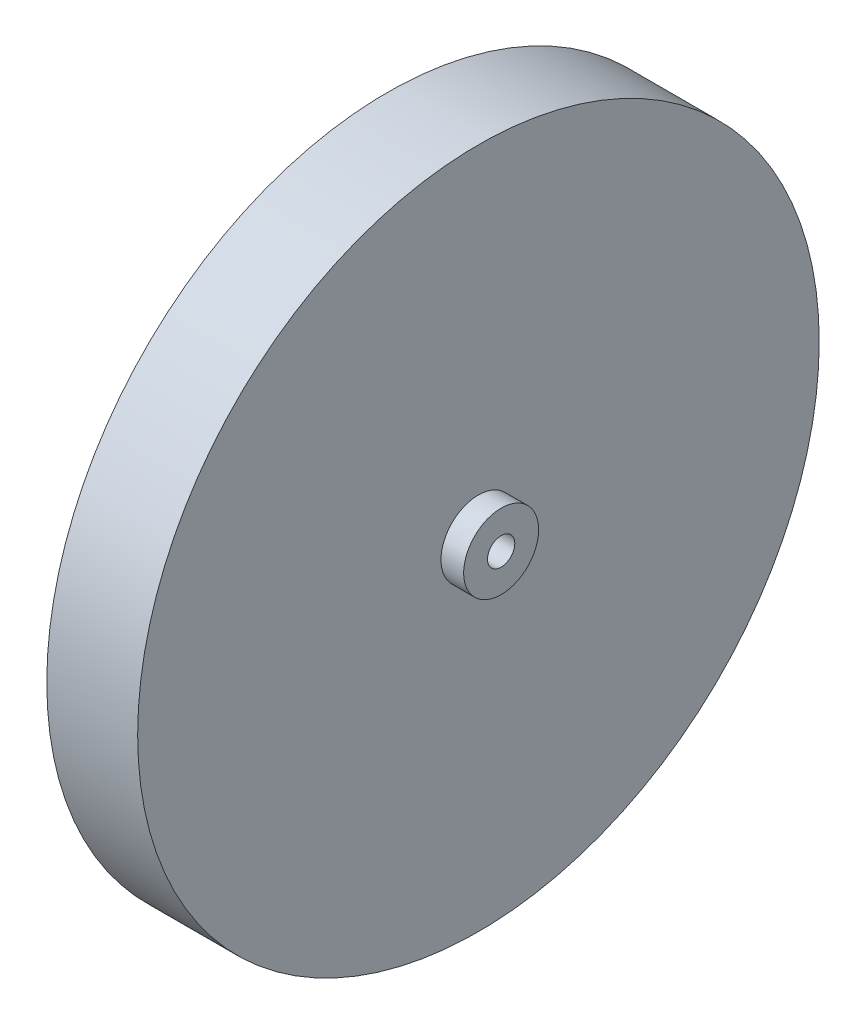
SolidWorks part; units mm, degrees
ref_plane "Front Plane" through (0, 0, 0) normal (0, 0, 1) x (1, 0, 0)
ref_plane "Top Plane" through (0, 0, 0) normal (0, 1, 0) x (1, 0, 0)
ref_plane "Right Plane" through (0, 0, 0) normal (1, 0, 0) x (0, 0, -1)
sketch "Sketch1" plane through (0, 0, 0) normal (1, 0, 0) x (0, 0, -1)
  circle A0 centre (0, 0) radius 38.1
  dimension "D1" = 76.2
extrude "Boss-Extrude1" add sketch "Sketch1" along normal blind 10.16
sketch "Sketch3" plane through (10.16, 0, 0) normal (1, 0, 0) x (0, 0, -1)
  circle A0 centre (0, 0) radius 4.191
  dimension "D1" = 8.382
extrude "Boss-Extrude2" add sketch "Sketch3" along normal blind 2.54
sketch "Sketch4" plane through (12.7, 0, 0) normal (1, 0, 0) x (0, 0, -1)
  circle A0 centre (0, 0) radius 1.524
  dimension "D1" = 3.048
extrude "Cut-Extrude1" cut sketch "Sketch4" against normal through all
sketch "Sketch5" plane through (0, 0, 0) normal (-1, 0, 0) x (0, 0, 1)
  circle A0 centre (0, 0) radius 22.86
  dimension "D1" = 45.72
extrude "Cut-Extrude2" cut sketch "Sketch5" against normal blind 3.81
sketch "Sketch6" plane through (3.81, 0, 0) normal (-1, 0, 0) x (0, 0, 1)
  circle A0 centre (0, 0) radius 12.7
  dimension "D1" = 25.4
extrude "Cut-Extrude3" cut sketch "Sketch6" against normal blind 2.54
sketch "Sketch7" plane through (6.35, 0, 0) normal (-1, 0, 0) x (0, 0, 1)
  circle A0 centre (0, 0) radius 6.731
  dimension "D1" = 13.462
extrude "Boss-Extrude3" add sketch "Sketch7" along normal blind 3.81
sketch "Sketch9" plane through (2.54, 0, 0) normal (-1, 0, 0) x (0, 0, 1)
  circle A0 centre (0, 0) radius 3.81
  dimension "D1" = 7.62
extrude "Cut-Extrude4" cut sketch "Sketch9" against normal blind 3.81
equation "\"wheel\"= 0.4"
equation "\"D1@Boss-Extrude1\"=\"wheel\""
